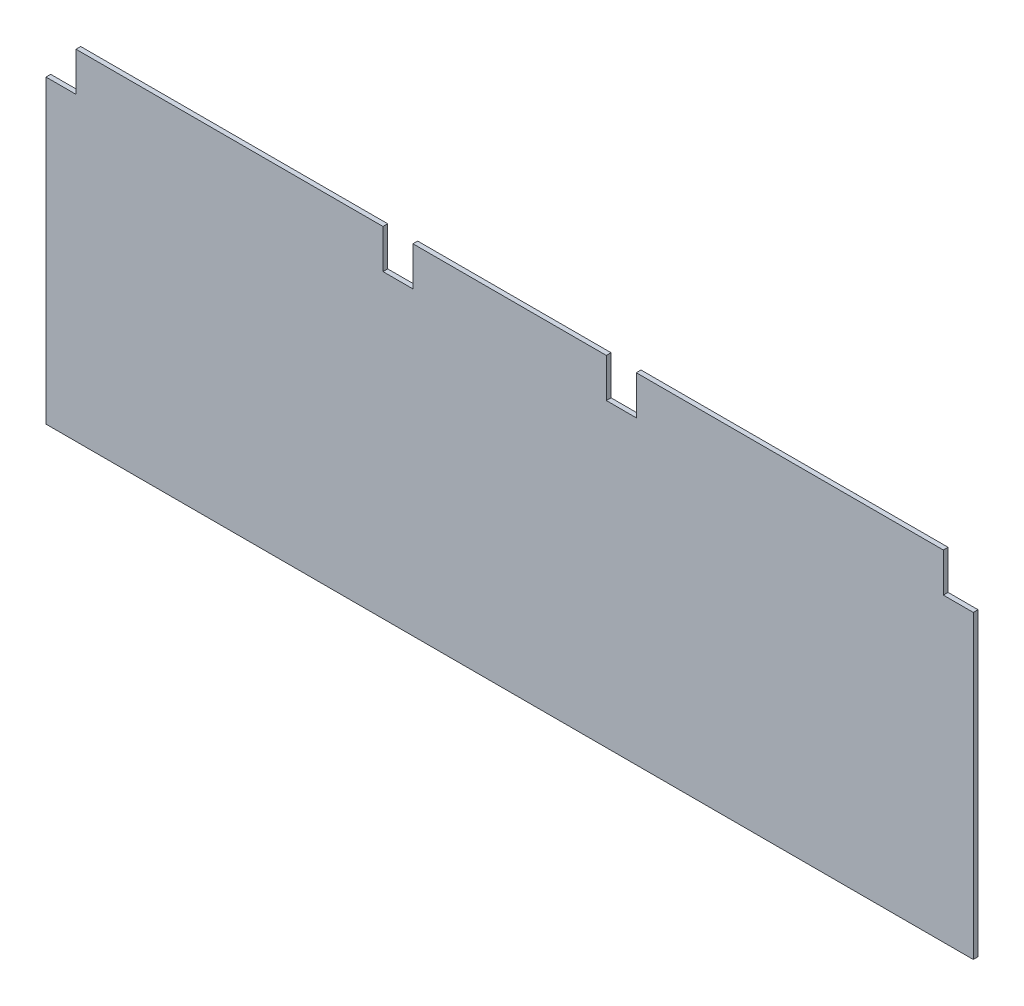
SolidWorks part; units mm, degrees
ref_plane "Alzado" through (0, 0, 0) normal (0, 0, 1) x (1, 0, 0)
ref_plane "Planta" through (0, 0, 0) normal (0, 1, 0) x (1, 0, 0)
ref_plane "Vista lateral" through (0, 0, 0) normal (1, 0, 0) x (0, 0, -1)
sketch "Croquis1" plane through (0, 0, 0) normal (0, 0, 1) x (1, 0, 0)
  line L1 (-98.2, -35.974) -> (98.2, -35.974)
  line L2 (-98.2, -35.974) -> (-98.2, 35.974)
  line L3 (-98.2, 35.974) -> (98.2, 35.974)
  line L4 (98.2, -35.974) -> (98.2, 35.974)
  line L5 (-98.2, -35.974) -> (98.2, 35.974) construction
  line L6 (-98.2, 35.974) -> (98.2, -35.974) construction
  point P0 (0, 0)
  dimension "D1" = 196.4
  dimension "D2" = 71.948
extrude "Saliente-Extruir1" add sketch "Croquis1" along normal blind 1 contours L4 L3 L2 L1
sketch "Croquis5" plane through (0, 0, 0) normal (0, 0, -1) x (-1, 0, 0)
  line L0 (98.2, 35.974) -> (-98.2, 35.974) construction
  line L1 (-98.2, 35.974) -> (-91.85, 35.974)
  line L2 (-98.2, 35.974) -> (-98.2, 27.696)
  line L3 (-98.2, 27.696) -> (-91.85, 27.696)
  line L4 (-91.85, 35.974) -> (-91.85, 27.696)
  line L5 (-26.83, 35.974) -> (-20.48, 35.974)
  line L6 (-26.83, 35.974) -> (-26.83, 27.696)
  line L7 (-26.83, 27.696) -> (-20.48, 27.696)
  line L8 (-20.48, 35.974) -> (-20.48, 27.696)
  line L10 (20.48, 35.974) -> (26.83, 35.974)
  line L11 (20.48, 35.974) -> (20.48, 27.696)
  line L12 (20.48, 27.696) -> (26.83, 27.696)
  line L13 (26.83, 35.974) -> (26.83, 27.696)
  line L14 (98.2, 35.974) -> (91.85, 35.974)
  line L15 (98.2, 35.974) -> (98.2, 27.696)
  line L16 (98.2, 27.696) -> (91.85, 27.696)
  line L17 (91.85, 35.974) -> (91.85, 27.696)
  dimension "D1" = 6.35
  dimension "D2" = 6.35
  dimension "D3" = 6.35
  dimension "D4" = 6.35
  dimension "D5" = 8.278
  dimension "D6" = 8.278
  dimension "D7" = 8.278
  dimension "D8" = 8.278
  dimension "D9" = 65.02
  dimension "D10" = 65.02
  dimension "D11" = 40.96
extrude "Cortar-Extruir2" cut sketch "Croquis5" against normal through all
equation "\"D6@Croquis5\"=\"D5@Croquis5\""
equation "\"D7@Croquis5\"=\"D5@Croquis5\""
equation "\"D8@Croquis5\"=\"D5@Croquis5\""
